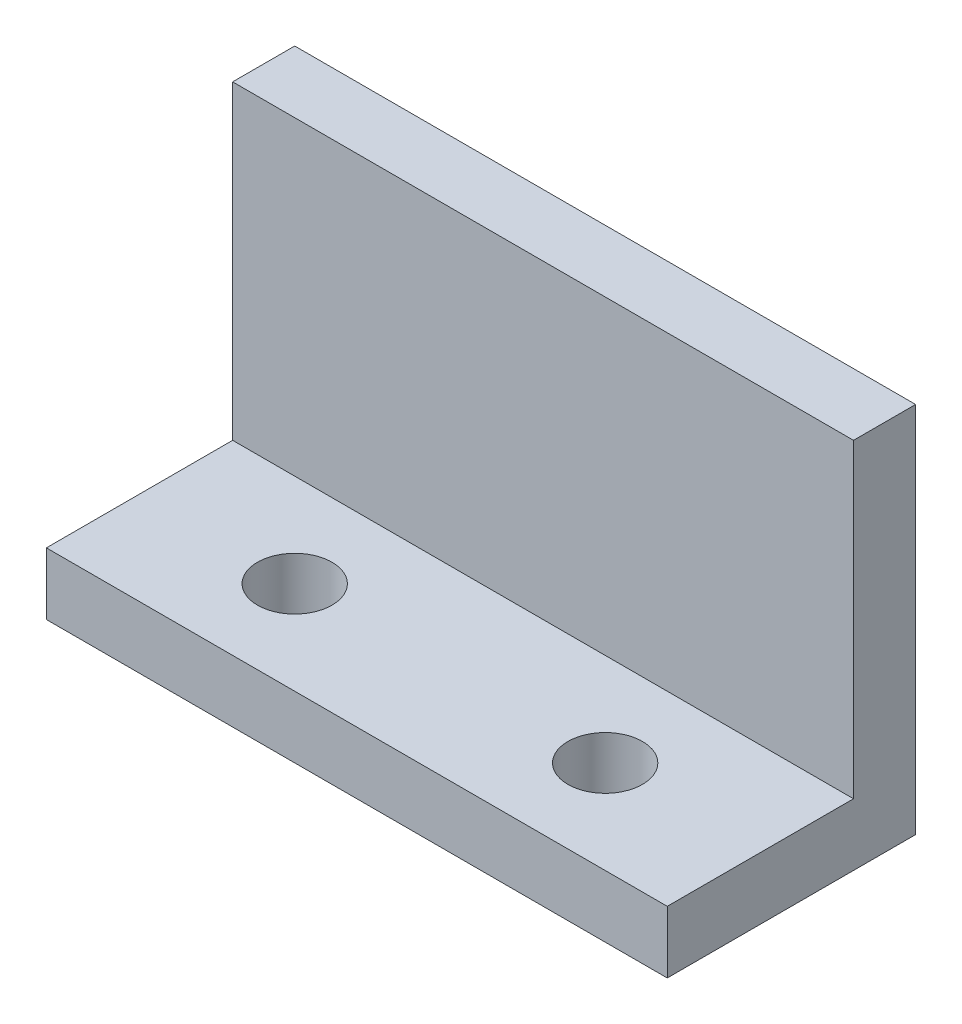
SolidWorks part; units mm, degrees
ref_plane "Płaszczyzna przednia" through (0, 0, 0) normal (0, 0, 1) x (1, 0, 0)
ref_plane "Płaszczyzna górna" through (0, 0, 0) normal (0, 1, 0) x (1, 0, 0)
ref_plane "Płaszczyzna prawa" through (0, 0, 0) normal (1, 0, 0) x (0, 0, -1)
sketch "Szkic1" plane through (0, 0, 0) normal (0, 0, 1) x (1, 0, 0)
  line L1 (-50, -30) -> (50, -30)
  line L2 (-50, -30) -> (-50, 30)
  line L3 (-50, 30) -> (50, 30)
  line L4 (50, -30) -> (50, 30)
  line L5 (-50, -30) -> (50, 30) construction
  line L6 (-50, 30) -> (50, -30) construction
  point P0 (0, 0)
  dimension "D1" = 100
  dimension "D2" = 60
extrude "Dodanie-wyciągnięcie1" add sketch "Szkic1" along normal blind 10
sketch "Szkic2" plane through (0, 0, 10) normal (0, 0, 1) x (1, 0, 0)
  line L0 (50, -30) -> (50, 30) construction
  line L1 (-50, -30) -> (50, -30)
  line L2 (-50, -30) -> (-50, -20)
  line L3 (-50, -20) -> (50, -20)
  line L4 (50, -30) -> (50, -20)
  dimension "D1" = 10
extrude "Dodanie-wyciągnięcie2" add sketch "Szkic2" along normal blind 30
hole_wizard "Otwór pod śrubę M101" positions "Szkic3" profile "Szkic4" hole size "M10" standard "Ansi Metric" end condition through all
sketch "Szkic3" plane through (0, -20, 0) normal (0, 1, 0) x (1, 0, 0)
  line L0 (50, -40) -> (-50, -40) construction
  line L1 (-50, -40) -> (-50, -10) construction
  point P0 (-25, -25)
  dimension "D1" = 15
  dimension "D2" = 25
sketch "Szkic4" plane through (-25, -20, 25) normal (1, 0, 0) x (0, 0, 1)
  line L0 (0, 0) -> (0, 10)
  line L1 (0, 10) -> (6, 10)
  line L2 (6, 10) -> (6, 0)
  line L5 (6, 0) -> (0, 0)
  line L11 (0, -6.35) -> (0, 107.95) construction
  dimension "Średnica otworu na wylot" = 12
  dimension "Głębokość otworu na wylot" = 10
pattern_linear "Szyk liniowy2" count 2 spacing 50 along (1, 0, 0) of "Otwór pod śrubę M101"
